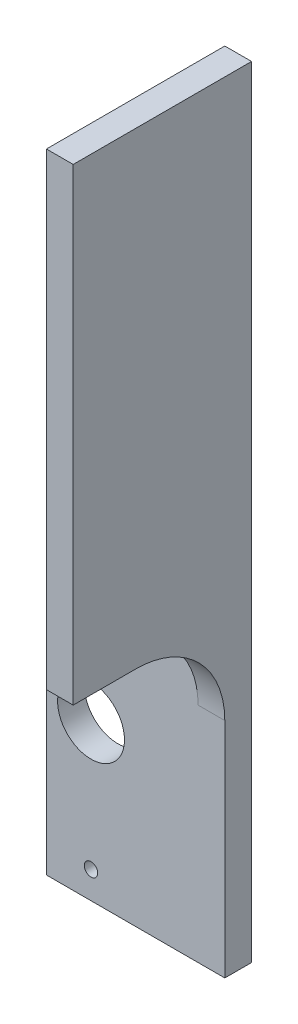
SolidWorks part; units mm, degrees
ref_plane "Front Plane" through (0, 0, 0) normal (0, 0, 1) x (1, 0, 0)
ref_plane "Top Plane" through (0, 0, 0) normal (0, 1, 0) x (1, 0, 0)
ref_plane "Right Plane" through (0, 0, 0) normal (1, 0, 0) x (0, 0, -1)
sketch "Sketch1" plane through (0, 0, 0) normal (0, 0, 1) x (1, 0, 0)
  line L0 (-10, 17.5) -> (0, 17.5) construction
  line L1 (0, 0) -> (-10, 0)
  line L2 (0, 0) -> (0, 35) construction
  line L3 (0, 35) -> (-10, 35)
  line L4 (-10, 0) -> (-10, 35)
  line L6 (0, 35) -> (10, 35)
  line L7 (0, 35) -> (0, 0) construction
  line L8 (0, 0) -> (10, 0)
  line L9 (10, 35) -> (10, 0)
  circle A0 centre (-5, 31.95) radius 0.75
  circle A1 centre (-5, 3.05) radius 0.75
  circle A2 centre (-5, 17.5) radius 3.75
  point P8 (-5, 35)
  dimension "D3" = 1.5
  dimension "D5" = 7.5
  dimension "D1" = 35
  dimension "D2" = 10
  dimension "D4" = 14.45
  dimension "D6" = 15
extrude "Boss-Extrude1" add sketch "Sketch1" along normal blind 3
sketch "Sketch2" plane through (0, 35, 0) normal (0, 1, 0) x (1, 0, 0)
  line L0 (10, 0) -> (-10, 0) construction
  line L5 (7, 0) -> (10, 0)
  line L6 (7, 0) -> (7, -20)
  line L7 (7, -20) -> (10, -20)
  line L8 (10, 0) -> (10, -20)
  point P7 (7.7427, -20)
  point P8 (0, 0)
  dimension "D1" = 20
  dimension "D2" = 3
extrude "Boss-Extrude2" add sketch "Sketch2" along normal blind 52.5
fillet "Fillet5" radius 10 2 edges at (8.5, 35, 3) (7, 35, 11.5)
